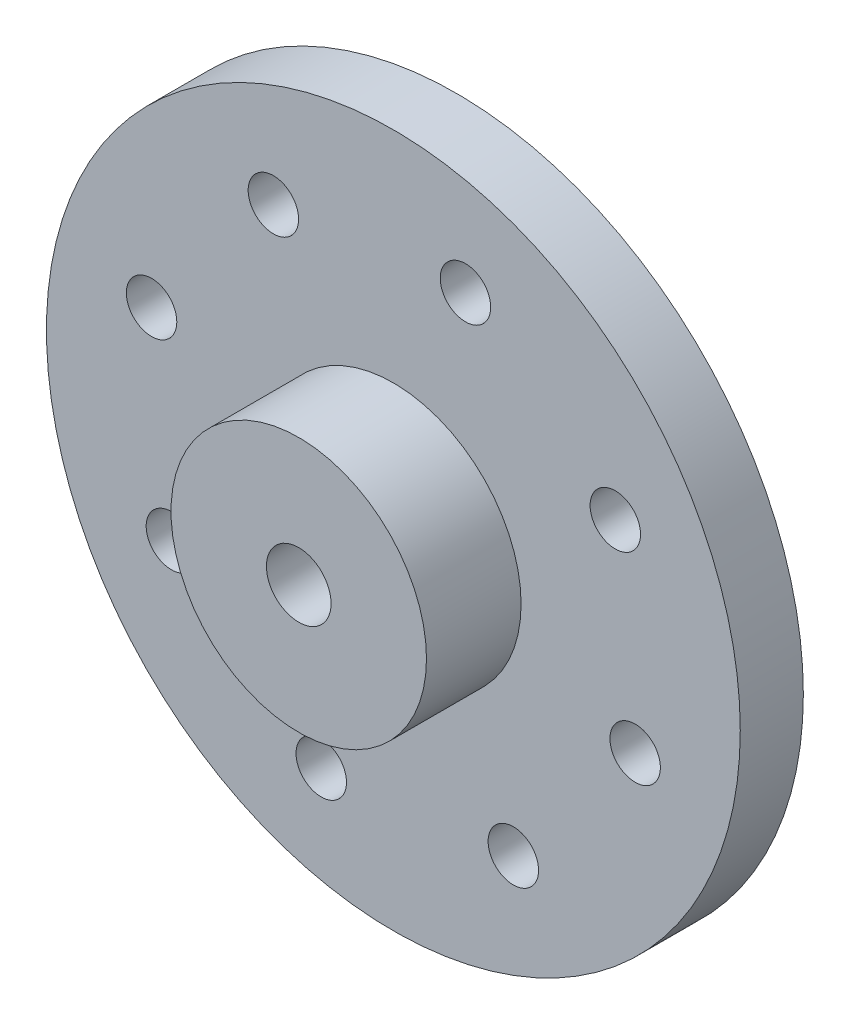
SolidWorks part; units mm, degrees
ref_plane "Front Plane" through (0, 0, 0) normal (0, 0, 1) x (1, 0, 0)
ref_plane "Top Plane" through (0, 0, 0) normal (0, 1, 0) x (1, 0, 0)
ref_plane "Right Plane" through (0, 0, 0) normal (1, 0, 0) x (0, 0, -1)
sketch "Sketch1" plane through (0, 0, 0) normal (0, 0, 1) x (1, 0, 0)
  circle A0 centre (0, 0) radius 11
  circle A1 centre (0, 0) radius 2.6699
  point P24 (0, 0)
  dimension "D1" = 22
  dimension "D2" = 5.3397
extrude "Boss-Extrude1" add sketch "Sketch1" along normal blind 2
sketch "Sketch2" plane through (0, 0, 2) normal (0, 0, 1) x (1, 0, 0)
  circle A1 centre (0, 0) radius 4.05
  dimension "D1" = 8.1
extrude "Boss-Extrude2" add sketch "Sketch2" along normal blind 3
sketch "Sketch3" plane through (0, 0, 0) normal (0, 0, -1) x (-1, 0, 0)
  circle A0 centre (0, 0) radius 2.6699
  circle A1 centre (0, 0) radius 4
extrude "Boss-Extrude3" add sketch "Sketch3" along normal blind 1
chamfer "Chamfer1" distance 0.6 angle 45 1 edges at (-4, 0, -1)
hole_wizard "M2 Tapped Hole1" positions "Sketch4" profile "Sketch5" tap size "M2" standard "ISO"
sketch "Sketch4" plane through (0, 0, 2) normal (0, 0, 1) x (1, 0, 0)
  point P0 (2.2862, 7.6664)
  point P9 (7.0375, 3.8044)
  point P10 (7.6664, -2.2862)
  point P11 (3.8044, -7.0375)
  point P12 (-2.2862, -7.6664)
  point P13 (-7.0375, -3.8044)
  point P14 (-7.6664, 2.2862)
  point P15 (-3.8044, 7.0375)
  point P16 (0, 0)
  dimension "D1" = 8
  dimension "D2" = 8
sketch "Sketch5" plane through (2.2862, 7.6664, 2) normal (1, 0, 0) x (0, -1, 0)
  line L0 (0, 0) -> (0, 3)
  line L1 (0, 3) -> (0.8, 3)
  line L2 (0.8, 3) -> (0.8, 0)
  line L5 (0.8, 0) -> (0, 0)
  line L11 (0, -6.35) -> (0, 107.95) construction
  dimension "Thru Tap Drill Dia." = 1.6
  dimension "Thru Tap Drill Depth" = 3
cosmetic thread "Hole Thread1" parameters "D2"=2
cosmetic thread "Hole Thread2" parameters "D2"=2
cosmetic thread "Hole Thread3" parameters "D2"=2
cosmetic thread "Hole Thread4" parameters "D2"=2
cosmetic thread "Hole Thread5" parameters "D2"=2
cosmetic thread "Hole Thread6" parameters "D2"=2
cosmetic thread "Hole Thread7" parameters "D2"=2
cosmetic thread "Hole Thread8" parameters "D2"=2
hole_wizard "M2.5 Tapped Hole1" positions "Sketch6" profile "Sketch7" tap size "M2.5" standard "ISO"
sketch "Sketch6" plane through (0, 0, 5) normal (0, 0, 1) x (1, 0, 0)
  point P0 (0, 0)
sketch "Sketch7" plane through (0, 0, 5) normal (1, 0, 0) x (0, -1, 0)
  line L0 (0, 0) -> (0, 6.9659)
  line L1 (0, 6.9659) -> (1.025, 6.35)
  line L2 (1.025, 6.35) -> (1.025, 0)
  line L5 (1.025, 0) -> (0, 0)
  line L10 (0, 6.9659) -> (-1.025, 6.35) construction
  line L11 (0, -6.35) -> (0, 107.95) construction
  dimension "Tap Drill Dia." = 2.05
  dimension "Tap Drill Depth" = 6.35
  dimension "Drill Angle" = 118
cosmetic thread "Hole Thread9" parameters "D1"=3, "D2"=2.5
